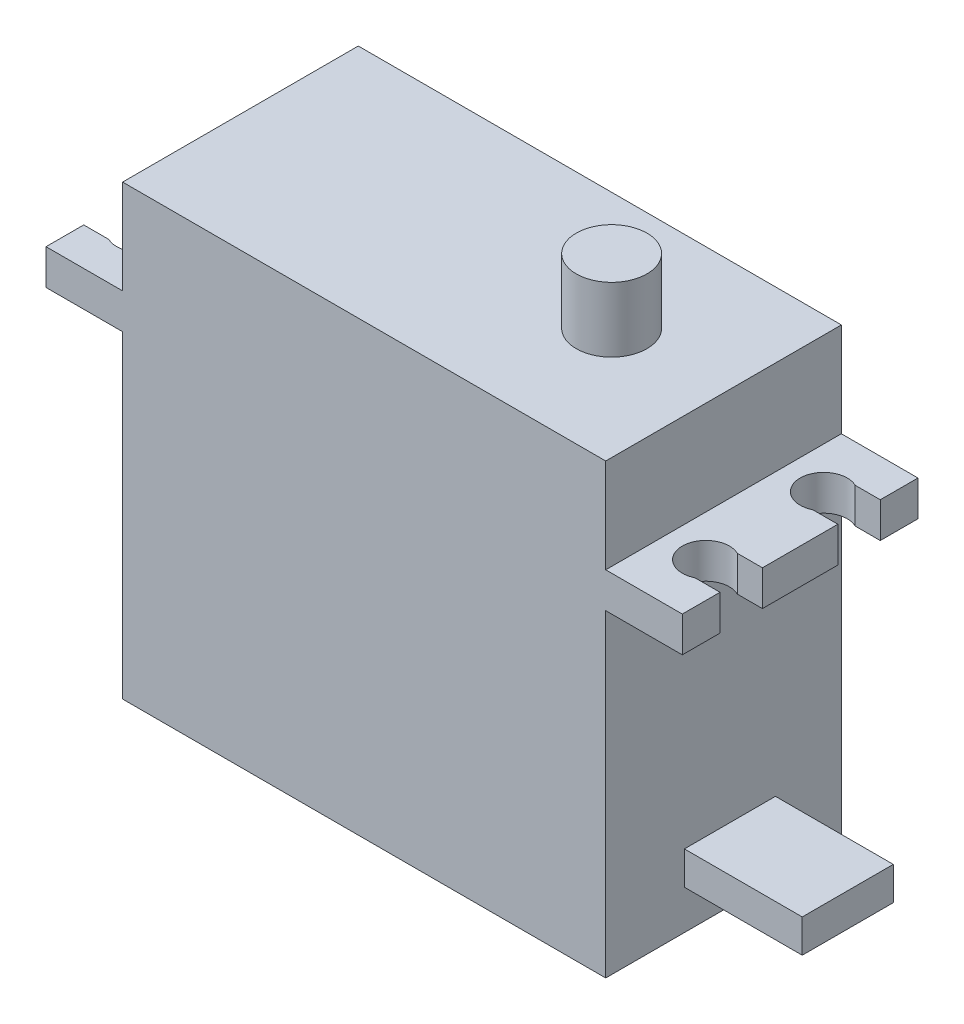
SolidWorks part; units mm, degrees
material "6061 合金"
ref_plane "前基準面" through (0, 0, 0) normal (0, 0, 1) x (1, 0, 0)
ref_plane "上基準面" through (0, 0, 0) normal (0, 1, 0) x (1, 0, 0)
ref_plane "右基準面" through (0, 0, 0) normal (1, 0, 0) x (0, 0, -1)
sketch "草圖1" plane through (0, 0, 0) normal (0, 1, 0) x (1, 0, 0)
  line L0 (0, 10) -> (0, -10) construction
  line L1 (-20.5, 10) -> (20.5, 10)
  line L2 (-20.5, 10) -> (-20.5, -10)
  line L3 (-20.5, -10) -> (20.5, -10)
  line L4 (20.5, 10) -> (20.5, -10)
  dimension "D1" = 20
  dimension "D2" = 41
extrude "伸長1" add sketch "草圖1" along normal blind 38
ref_plane "平面1" through (0, 27, 0) normal (0, 1, 0) x (-1, 0, 0)
sketch "草圖2" plane through (0, 27, 0) normal (0, 1, 0) x (-1, 0, 0)
  line L0 (-27, 0) -> (27, 0) construction
  line L1 (-27, -10) -> (27, -10)
  line L2 (-27, -10) -> (-27, 10)
  line L3 (-27, 10) -> (27, 10)
  line L4 (27, -10) -> (27, 10)
  dimension "D1" = 54
extrude "伸長2" add sketch "草圖2" along normal blind 3
sketch "草圖3" plane through (0, 30, 0) normal (0, 1, 0) x (-1, 0, 0)
  line L0 (-27, 0) -> (0, 0) construction
  line L1 (-27, 10) -> (-27, -10) construction
  line L2 (0, 0) -> (0, 10.1) construction
  line L4 (-24, 5) -> (-25.7349, 5) construction
  line L5 (-27, 3.2) -> (-24.8718, 3.2)
  line L6 (-27, 3.2) -> (-27, 6.8)
  line L7 (-27, 6.8) -> (-24.8718, 6.8)
  line L8 (-27, -6.8) -> (-24.8718, -6.8)
  line L9 (-27, -3.2) -> (-27, -6.8)
  line L10 (-27, -3.2) -> (-24.8718, -3.2)
  line L11 (27, -3.2) -> (24.8718, -3.2)
  line L12 (27, -3.2) -> (27, -6.8)
  line L13 (27, -6.8) -> (24.8718, -6.8)
  line L14 (27, 6.8) -> (24.8718, 6.8)
  line L15 (27, 3.2) -> (24.8718, 3.2)
  line L16 (27, 3.2) -> (27, 6.8)
  arc A0 (-24.8718, 3.2) -> (-24.8718, 6.8) centre (-24, 5) ccw
  arc A1 (-24.8718, -3.2) -> (-24.8718, -6.8) centre (-24, -5) cw
  arc A2 (24.8718, -3.2) -> (24.8718, -6.8) centre (24, -5) ccw
  arc A3 (24.8718, 3.2) -> (24.8718, 6.8) centre (24, 5) cw
  dimension "D2" = 2
  dimension "D3" = 10
  dimension "D4" = 48
  dimension "D1" = 3.6
extrude "除料-伸長1" cut sketch "草圖3" against normal up to next
sketch "草圖4" plane through (0, 30, 0) normal (0, 1, 0) x (-1, 0, 0)
  line L0 (-27, 0) -> (27, 0) construction
  line L1 (-27, 3.2) -> (-27, -3.2) construction
  line L2 (27, -3.2) -> (27, 3.2) construction
  line L3 (27, 0) -> (24, 5) construction
  line L4 (24, 5) -> (24, -5) construction
  circle A0 centre (-11, 0) radius 7.5
  dimension "D1" = 35
  dimension "D2" = 15
extrude "伸長3" add sketch "草圖4" along normal blind 3
sketch "草圖5" plane through (0, 38, 0) normal (0, 1, 0) x (-1, 0, 0)
  line L0 (-27, 3.2) -> (-27, -3.2) construction
  circle A0 centre (-11, 0) radius 3
  dimension "D1" = 6
  dimension "D2" = 16
extrude "伸長4" add sketch "草圖5" along normal blind 5.5
sketch "草圖6" plane through (20.5, 0, 0) normal (1, 0, 0) x (0, 0, -1)
  line L1 (-3.3218, 6.149) -> (4.405, 6.149)
  line L2 (-3.3218, 6.149) -> (-3.3218, 3.3327)
  line L3 (-3.3218, 3.3327) -> (4.405, 3.3327)
  line L4 (4.405, 6.149) -> (4.405, 3.3327)
extrude "伸長5" add sketch "草圖6" along normal blind 10
